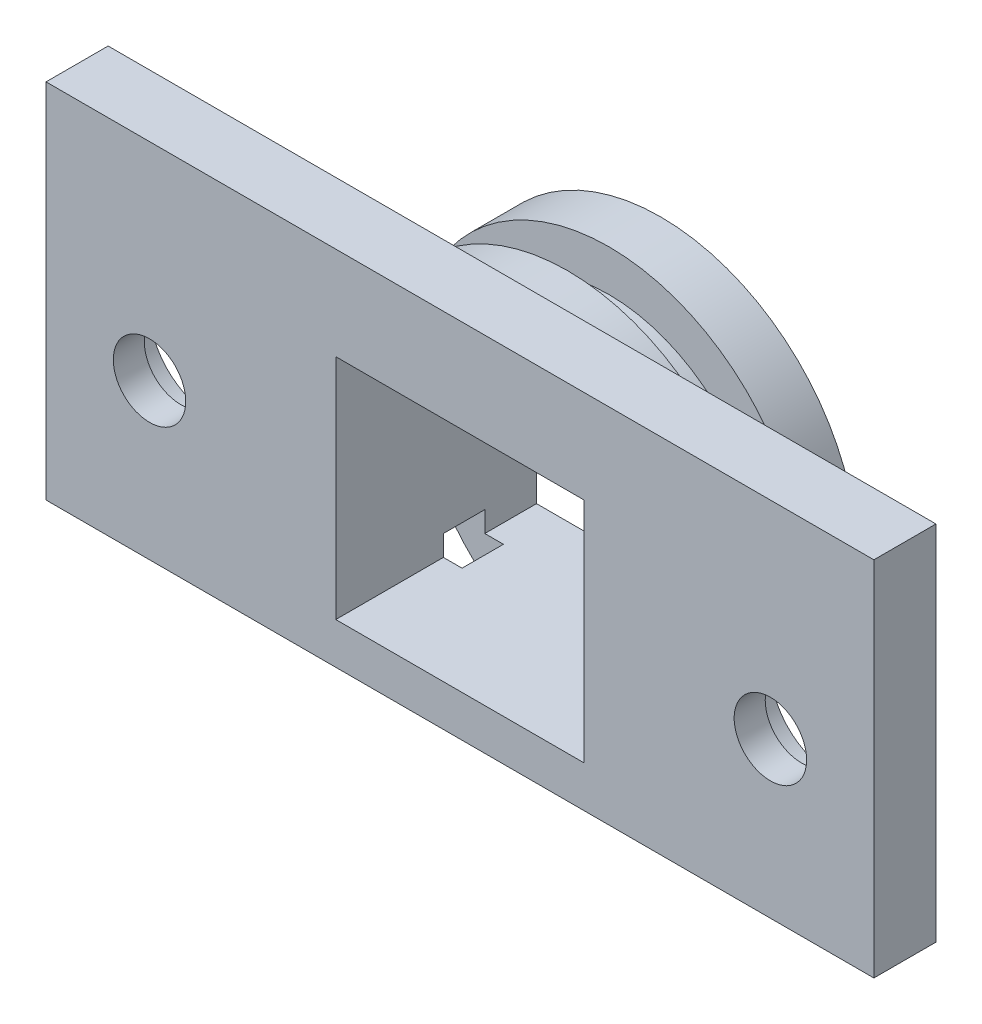
SolidWorks part; units mm, degrees
ref_plane "Front Plane" through (0, 0, 0) normal (0, 0, 1) x (1, 0, 0)
ref_plane "Top Plane" through (0, 0, 0) normal (0, 1, 0) x (1, 0, 0)
ref_plane "Right Plane" through (0, 0, 0) normal (1, 0, 0) x (0, 0, -1)
sketch "Sketch2" plane through (0, 0, 0) normal (0, 0, 1) x (1, 0, 0)
  line L0 (-5.831, -7.5) -> (5.831, -7.5)
  arc A0 (5.831, -7.5) -> (-5.831, -7.5) centre (0, 0) ccw
  dimension "D1" = 9.5
  dimension "D2" = 17
extrude "Boss-Extrude1" add sketch "Sketch2" against normal blind 2.2
sketch "Sketch3" plane through (0, 0, -2.2) normal (0, 0, -1) x (-1, 0, 0)
  line L0 (5.831, -7.5) -> (-5.831, -7.5) construction
  circle A0 centre (0, 0) radius 7.5
extrude "Boss-Extrude2" add sketch "Sketch3" along normal blind 2
sketch "Sketch4" plane through (0, 0, -4.2) normal (0, 0, -1) x (-1, 0, 0)
  line L3 (-5.831, -7.5) -> (5.831, -7.5)
  line L4 (-5.831, -7.5) -> (5.831, -7.5)
  arc A3 (5.831, -7.5) -> (-5.831, -7.5) centre (0, 0) ccw
  arc A4 (5.831, -7.5) -> (-5.831, -7.5) centre (0, 0) ccw
  dimension "D1" = 0
extrude "Boss-Extrude3" add sketch "Sketch4" along normal blind 2.5
sketch "Sketch5" plane through (0, 0, -6.7) normal (0, 0, -1) x (-1, 0, 0)
  line L1 (-6, -5.5) -> (6, -5.5)
  line L2 (-6, -5.5) -> (-6, 5.5)
  line L3 (-6, 5.5) -> (6, 5.5)
  line L4 (6, -5.5) -> (6, 5.5)
  line L5 (-6, -5.5) -> (6, 5.5) construction
  line L6 (-6, 5.5) -> (6, -5.5) construction
  point P0 (0, 0)
  dimension "D1" = 12
  dimension "D2" = 11
extrude "Cut-Extrude1" cut sketch "Sketch5" against normal through all contours L3 L4 L1 L2
sketch "Sketch6" plane through (0, 0, 0) normal (0, 0, 1) x (1, 0, 0)
  line L1 (-20, -10) -> (20, -10)
  line L2 (-20, -10) -> (-20, 10)
  line L3 (-20, 10) -> (20, 10)
  line L4 (20, -10) -> (20, 10)
  line L5 (-20, -10) -> (20, 10) construction
  line L6 (-20, 10) -> (20, -10) construction
  line L8 (6, -5.5) -> (6, 5.5) construction
  line L9 (6, -5.5) -> (-6, -5.5) construction
  line L10 (-6, -5.5) -> (-6, 5.5) construction
  line L11 (6, 5.5) -> (-6, 5.5) construction
  line L12 (6, -5.5) -> (6, 5.5)
  line L13 (6, -5.5) -> (-6, -5.5)
  line L14 (-6, -5.5) -> (-6, 5.5)
  line L15 (6, 5.5) -> (-6, 5.5)
  point P0 (0, 0)
  dimension "D1" = 20
  dimension "D2" = 40
extrude "Boss-Extrude4" add sketch "Sketch6" along normal blind 3
sketch "Sketch7" plane through (0, 0, 3) normal (0, 0, 1) x (1, 0, 0)
  line L0 (-15, 0) -> (15, 0) construction
  circle A0 centre (-15, 0) radius 1.75
  circle A1 centre (15, 0) radius 1.75
  dimension "D1" = 3.5
  dimension "D2" = 30
extrude "Cut-Extrude2" cut sketch "Sketch7" against normal through all
sketch "Sketch8" plane through (0, 0, 0) normal (0, 0, -1) x (-1, 0, 0)
  circle A0 centre (15, 0) radius 3
  circle A1 centre (-15, 0) radius 3
  dimension "D1" = 6
extrude "Cut-Extrude3" cut sketch "Sketch8" against normal blind 1.5
sketch "Sketch9" plane through (0, 0, -6.7) normal (0, 0, -1) x (-1, 0, 0)
  line L0 (20, 10) -> (20, -10) construction
  line L1 (20, -7.5) -> (-20, -7.5)
  line L2 (20, -7.5) -> (20, -10)
  line L3 (20, -10) -> (-20, -10)
  line L4 (-20, -7.5) -> (-20, -10)
  line L5 (-5.831, -7.5) -> (5.831, -7.5) construction
extrude "Cut-Extrude4" cut sketch "Sketch9" against normal through all
